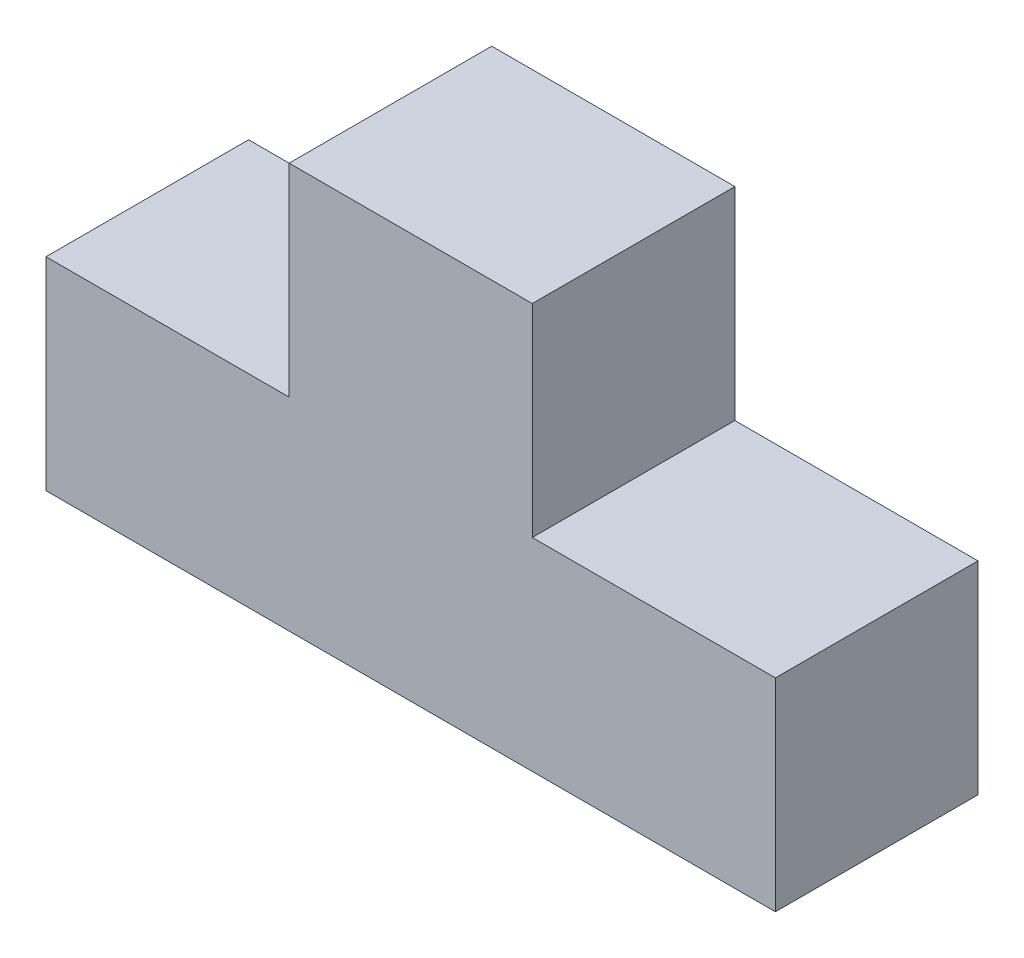
SolidWorks part; units mm, degrees
ref_plane "Front Plane" through (0, 0, 0) normal (0, 0, 1) x (1, 0, 0)
ref_plane "Top Plane" through (0, 0, 0) normal (0, 1, 0) x (1, 0, 0)
ref_plane "Right Plane" through (0, 0, 0) normal (1, 0, 0) x (0, 0, -1)
sketch "Sketch1" plane through (0, 0, 0) normal (0, 0, 1) x (1, 0, 0)
  line L0 (0, 0) -> (90, 0)
  line L1 (90, 0) -> (90, 25)
  line L2 (90, 25) -> (60, 25)
  line L3 (60, 25) -> (60, 50)
  line L4 (60, 50) -> (30, 50)
  line L5 (30, 50) -> (30, 25)
  line L6 (30, 25) -> (0, 25)
  line L7 (0, 25) -> (0, 0)
  dimension "D1" = 90
  dimension "D2" = 25
  dimension "D3" = 30
  dimension "D4" = 25
  dimension "D5" = 30
  dimension "D6" = 25
extrude "Boss-Extrude1" add sketch "Sketch1" along normal blind 25
